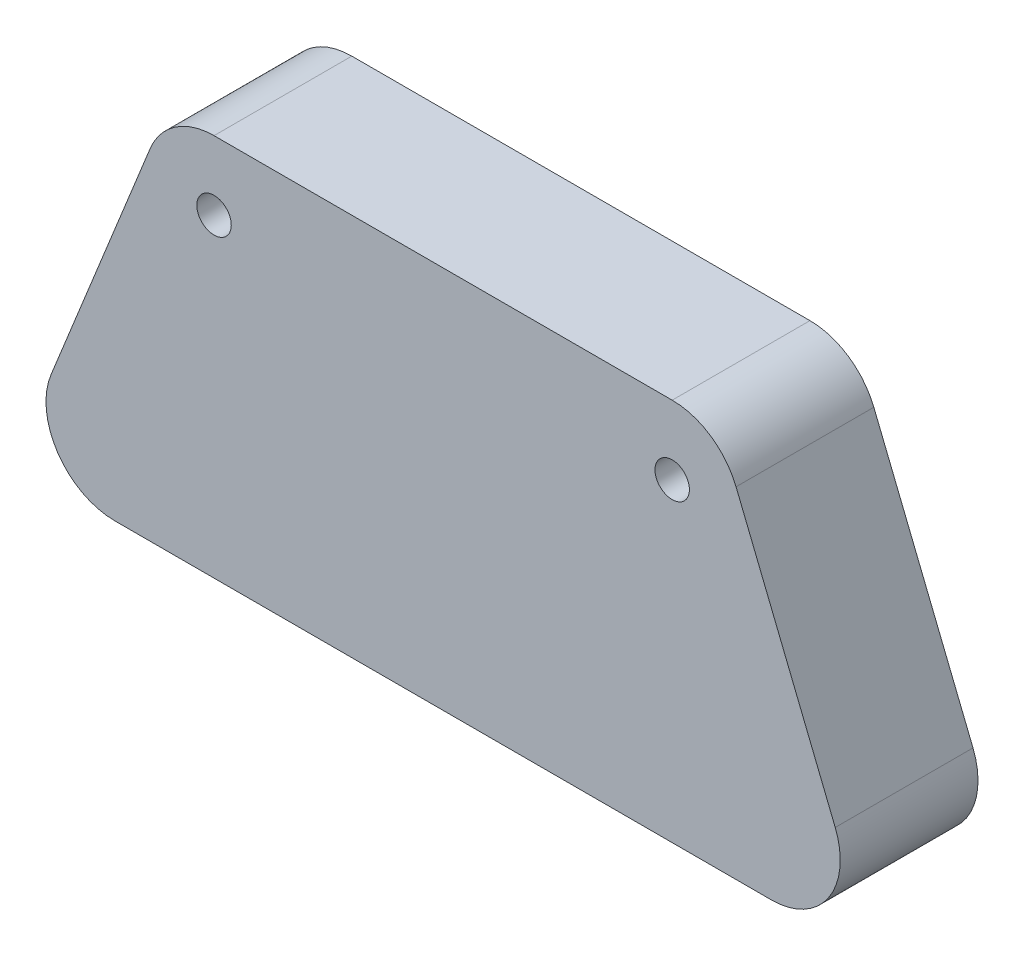
SolidWorks part; units mm, degrees
ref_plane "Front Plane" through (0, 0, 0) normal (0, 0, 1) x (1, 0, 0)
ref_plane "Top Plane" through (0, 0, 0) normal (0, 1, 0) x (1, 0, 0)
ref_plane "Right Plane" through (0, 0, 0) normal (1, 0, 0) x (0, 0, -1)
sketch "Sketch2" plane through (0, 0, 0) normal (0, 0, 1) x (1, 0, 0)
  line L0 (-8.8081, 12.6209) -> (24.4468, 12.6209)
  line L1 (29.0827, 9.4939) -> (36.2807, -8.3216)
  line L2 (-16.006, -15.1946) -> (31.6448, -15.1946)
  line L3 (-13.444, 9.4939) -> (-20.6419, -8.3216)
  arc A0 (-20.6419, -8.3216) -> (-16.006, -15.1946) centre (-16.006, -10.1946) ccw
  arc A1 (36.2807, -8.3216) -> (31.6448, -15.1946) centre (31.6448, -10.1946) cw
  arc A2 (24.4468, 12.6209) -> (29.0827, 9.4939) centre (24.4468, 7.6209) cw
  arc A3 (-8.8081, 12.6209) -> (-13.444, 9.4939) centre (-8.8081, 7.6209) ccw
  circle A4 centre (-8.8081, 7.6209) radius 1.25
  circle A5 centre (24.4468, 7.6209) radius 1.25
  dimension "D1" = 5
extrude "Boss-Extrude1" add sketch "Sketch2" along normal blind 10
